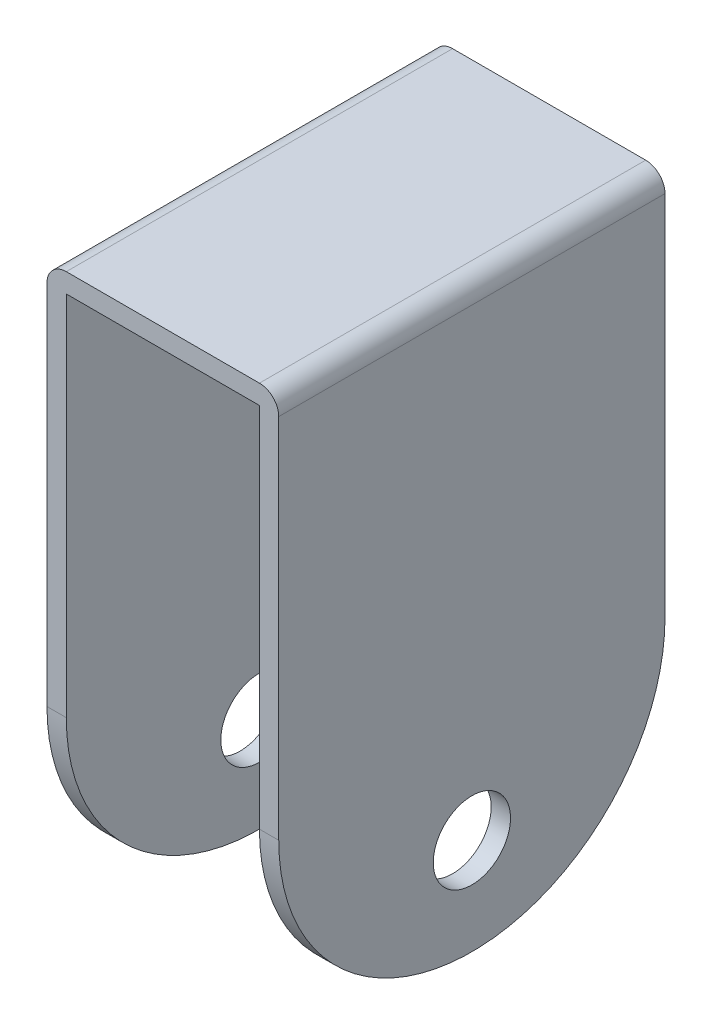
SolidWorks part; units mm, degrees
ref_plane "Front Plane" through (0, 0, 0) normal (0, 0, 1) x (1, 0, 0)
ref_plane "Top Plane" through (0, 0, 0) normal (0, 1, 0) x (1, 0, 0)
ref_plane "Right Plane" through (0, 0, 0) normal (1, 0, 0) x (0, 0, -1)
sketch "Sketch1" plane through (0, 0, 0) normal (1, 0, 0) x (0, 0, -1)
  line L1 (0, 0) -> (60, 0)
  line L2 (0, 0) -> (0, -60)
  line L4 (60, 0) -> (60, -60)
  arc A0 (60, -60) -> (0, -60) centre (30, -60) cw
  circle A1 centre (30, -75) radius 6
  dimension "D3" = 30
  dimension "D4" = 12
  dimension "D5" = 75
  dimension "D1" = 60
  dimension "D2" = 60
extrude "Boss-Extrude1" add sketch "Sketch1" against normal blind 3
sketch "Sketch2" plane through (-3, 0, 0) normal (-1, 0, 0) x (0, 0, 1)
  line L0 (0, 0) -> (0, -60) construction
  line L1 (-60, 0) -> (0, 0)
  line L2 (-60, 0) -> (-60, -3)
  line L3 (-60, -3) -> (0, -3)
  line L4 (0, 0) -> (0, -3)
  dimension "D1" = 3
extrude "Boss-Extrude2" add sketch "Sketch2" along normal blind 30
sketch "Sketch3" plane through (-33, 0, 0) normal (-1, 0, 0) x (0, 0, 1)
  line L0 (0, -3) -> (0, -60) construction
  line L1 (-60, 0) -> (0, 0)
  line L2 (-60, 0) -> (-60, -60)
  line L4 (0, 0) -> (0, -60)
  arc A0 (0, -60) -> (-60, -60) centre (-30, -60) cw
  circle A1 centre (-30, -75) radius 6
  dimension "D1" = 60
extrude "Boss-Extrude4" add sketch "Sketch3" along normal blind 3
fillet "Fillet1" radius 3 2 edges at (0, 0, -30) (-36, 0, -30)
